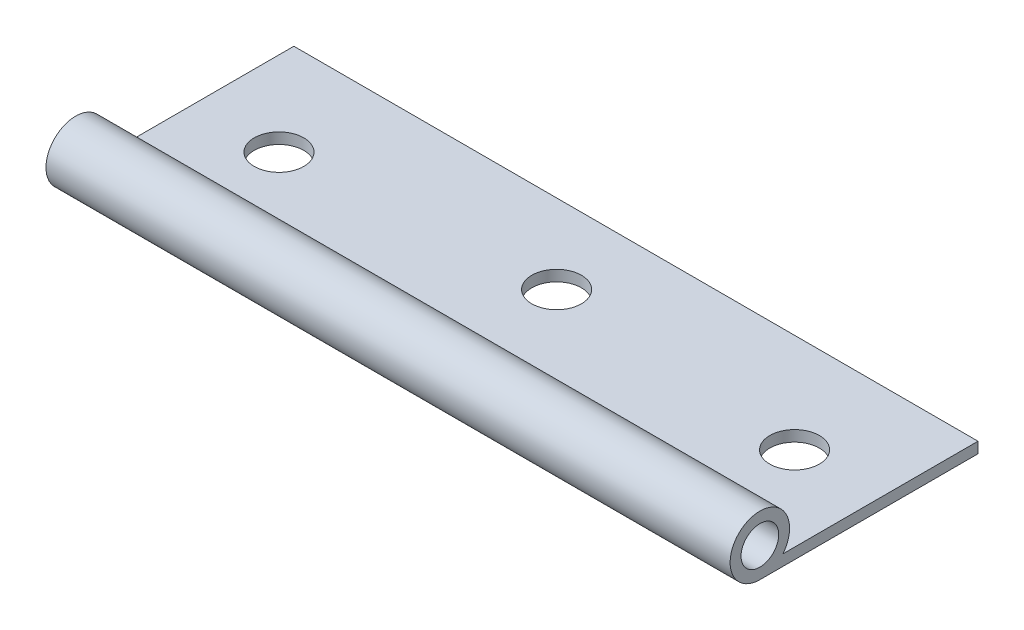
SolidWorks part; units mm, degrees
material "AISI 304"
ref_plane "Front" through (0, 0, 0) normal (0, 0, 1) x (1, 0, 0)
ref_plane "Top" through (0, 0, 0) normal (0, 1, 0) x (1, 0, 0)
ref_plane "Right" through (0, 0, 0) normal (1, 0, 0) x (0, 0, -1)
sketch "草图1" plane through (0, 0, 0) normal (1, 0, 0) x (0, 0, -1)
  line L0 (0, 0) -> (19, 0)
  line L1 (19, 0) -> (19, -1.1)
  line L2 (19, -1.1) -> (0, -1.1)
  line L3 (0, -1.1) -> (0, 5.2282) construction
  line L4 (0, -1.1) -> (-3, -1.1)
  line L5 (0, 0) -> (-0.6784, 0)
  arc A0 (-0.6784, 0) -> (-3, -1.1) centre (-3, 1.9) ccw
  circle A1 centre (-3, 1.9) radius 1.9
  dimension "D3" = 6
  dimension "D1" = 19
  dimension "D2" = 1.1
extrude "凸台-拉伸1" add sketch "草图1" along normal blind 69
sketch "草图2" plane through (0, 0, 0) normal (0, 1, 0) x (1, 0, 0)
  line L0 (0, 9) -> (69, 9) construction
  line L1 (0, 19) -> (0, -0.6784) construction
  line L2 (69, 19) -> (69, -0.6784) construction
  line L3 (69, 19) -> (0, 19) construction
  line L4 (34.5, 19) -> (34.5, -12.902) construction
  circle A0 centre (8.5, 9) radius 2.5
  circle A1 centre (60.5, 9) radius 2.5
  circle A2 centre (34.5, 11) radius 2.5
  dimension "D1" = 5
  dimension "D4" = 8
  dimension "D2" = 10
  dimension "D3" = 8.5
extrude "切除-拉伸1" cut sketch "草图2" against normal through all
